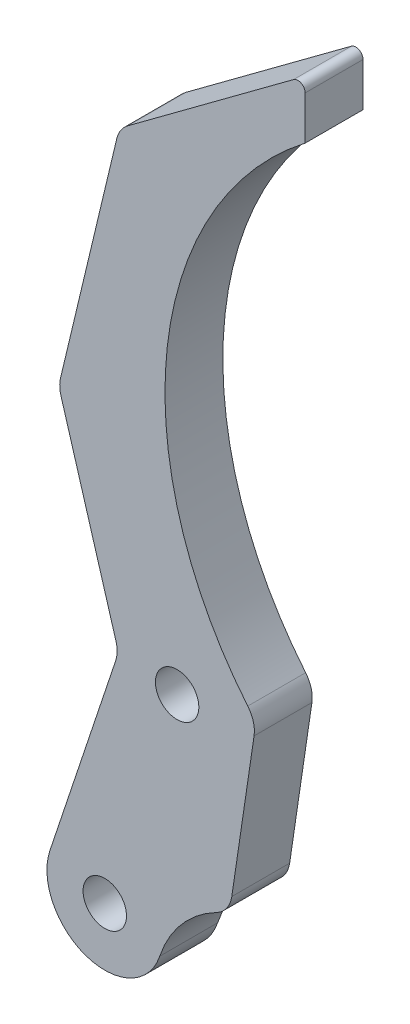
SolidWorks part; units mm, degrees
ref_plane "前视基准面" through (0, 0, 0) normal (0, 0, 1) x (1, 0, 0)
ref_plane "上视基准面" through (0, 0, 0) normal (0, 1, 0) x (1, 0, 0)
ref_plane "右视基准面" through (0, 0, 0) normal (1, 0, 0) x (0, 0, -1)
sketch "草图1" plane through (0, 0, 0) normal (0, 0, 1) x (1, 0, 0)
  line L1 (-44.759, 0) -> (37.6123, 0) construction
  line L2 (0, 0) -> (0, 68.6572) construction
  line L3 (15.4812, 24.7175) -> (6.2807, 1.4721) construction
  line L4 (22.9197, 21.7734) -> (13.7193, -1.4721) construction
  line L5 (22.9952, 24.5104) -> (15.4057, 21.9805) construction
  line L6 (8.8834, 38.4304) -> (10.4236, 28.044) construction
  line L8 (22.9952, 24.5104) -> (18.4512, 38.1424) construction
  line L9 (18.4316, 39.345) -> (22.233, 52.1252) construction
  line L10 (22.2613, 53.1601) -> (18.3728, 69.4382) construction
  line L11 (11.411, 39.3495) -> (2.2105, 16.1041) construction
  line L12 (16.9899, 37.1414) -> (7.7895, 13.8959) construction
  line L13 (17.619, 70.5799) -> (6.1506, 79.0862) construction
  line L14 (5.3527, 78.6846) -> (5.3527, 75.678) construction
  line L15 (-15.4812, 24.7175) -> (-6.2807, 1.4721) construction
  line L16 (-22.9197, 21.7734) -> (-13.7193, -1.4721) construction
  line L17 (-16.9899, 37.1414) -> (-7.7895, 13.8959) construction
  line L18 (-11.411, 39.3495) -> (-2.2105, 16.1041) construction
  line L19 (-8.8834, 38.4304) -> (-10.4236, 28.044)
  line L20 (-22.9952, 24.5104) -> (-18.4512, 38.1424)
  line L25 (-18.4316, 39.345) -> (-22.233, 52.1252)
  line L26 (-5, 15) -> (-10, 0) construction
  line L27 (5, 15) -> (10, 0) construction
  line L28 (14.2005, 38.2455) -> (19.2005, 23.2455) construction
  line L29 (-22.2613, 53.1601) -> (-18.3728, 69.4382)
  line L30 (-17.619, 70.5799) -> (-6.1506, 79.0862)
  line L31 (-5.3527, 78.6846) -> (-5.3527, 75.678)
  line L32 (-9.9581, 55.9149) -> (14.9371, 53.6276) construction
  circle A0 centre (-10, 0) radius 10 construction
  circle A4 centre (0, 55) radius 15 construction
  circle A5 centre (10, 0) radius 4 construction
  circle A6 centre (10, 0) radius 10 construction
  arc A14 (15.4057, 21.9805) -> (10.5848, 26.9564) centre (7.8163, 19.4507) ccw construction
  circle A16 centre (19.2005, 23.2455) radius 1.5 construction
  circle A17 centre (19.2005, 23.2455) radius 4 construction
  circle A18 centre (5, 15) radius 3 construction
  arc A19 (9.3195, 39.9972) -> (5.3527, 75.678) centre (-9.9581, 55.9149) ccw construction
  circle A20 centre (14.2005, 38.2455) radius 3 construction
  circle A21 centre (-10, 0) radius 4 construction
  circle A22 centre (-19.2005, 23.2455) radius 1.5
  arc A23 (-22.9952, 24.5104) -> (-15.4057, 21.9805) centre (-19.2005, 23.2455) ccw
  arc A24 (-15.4057, 21.9805) -> (-11.4848, 26.56) centre (-7.8163, 19.4507) cw
  circle A25 centre (-14.2005, 38.2455) radius 3 construction
  circle A26 centre (-5, 15) radius 3 construction
  circle A28 centre (-14.2005, 38.2455) radius 1.5
  circle A29 centre (-5, 15) radius 1.5 construction
  circle A30 centre (5, 15) radius 1.5 construction
  circle A31 centre (14.2005, 38.2455) radius 1.5 construction
  arc A33 (-11.4848, 26.56) -> (-10.4236, 28.044) centre (-12.4019, 28.3373) ccw
  arc A40 (6.1506, 79.0862) -> (5.3527, 78.6846) centre (5.8527, 78.6846) ccw construction
  arc A41 (11.4848, 26.56) -> (10.4236, 28.044) centre (12.4019, 28.3373) cw construction
  arc A42 (8.8834, 38.4304) -> (9.3195, 39.9972) centre (10.8617, 38.7237) cw construction
  arc A43 (-9.3195, 39.9972) -> (-5.3527, 75.678) centre (9.9581, 55.9149) cw
  arc A44 (18.4512, 38.1424) -> (18.4316, 39.345) centre (20.3486, 38.7748) cw construction
  arc A45 (22.233, 52.1252) -> (22.2613, 53.1601) centre (20.316, 52.6954) ccw construction
  arc A46 (18.3728, 69.4382) -> (17.619, 70.5799) centre (16.4275, 68.9735) ccw construction
  arc A47 (-6.1506, 79.0862) -> (-5.3527, 78.6846) centre (-5.8527, 78.6846) cw
  arc A48 (-8.8834, 38.4304) -> (-9.3195, 39.9972) centre (-10.8617, 38.7237) ccw
  arc A49 (-18.4512, 38.1424) -> (-18.4316, 39.345) centre (-20.3486, 38.7748) ccw
  arc A50 (-22.233, 52.1252) -> (-22.2613, 53.1601) centre (-20.316, 52.6954) cw
  arc A51 (-18.3728, 69.4382) -> (-17.619, 70.5799) centre (-16.4275, 68.9735) cw
  point P71 (31.2517, 19.1606)
  point P72 (-18.5078, 23.7319)
  point P73 (23.0842, 24.6753)
  point P93 (5.3527, 79.678)
  point P96 (8.7498, 39.3313)
  point P99 (18.2518, 38.7406)
  point P102 (22.3858, 52.6388)
  point P105 (18.2036, 70.1462)
  point P109 (-5.3527, 79.678)
  point P112 (-8.7498, 39.3313)
  point P115 (-18.2518, 38.7406)
  point P118 (-10.5848, 26.9564)
  point P122 (-22.3858, 52.6388)
  point P125 (-18.2036, 70.1462)
  dimension "D1" = 30
  dimension "D3" = 20
  dimension "D4" = 25
  dimension "D5" = 8
  dimension "D6" = 3
  dimension "D7" = 2
  dimension "D8" = 8
  dimension "D13" = 25
  dimension "D20" = 140
  dimension "D21" = 6
  dimension "D27" = 3
  dimension "D29" = 0.5
  dimension "D28" = 16
  dimension "D30" = 2
  dimension "D31" = 55
  dimension "D14" = 4
  dimension "D12" = 10.5
  dimension "D18" = 150
  dimension "D10" = 0.5
  dimension "D26" = 2
  dimension "D9" = 11
  dimension "D11" = 15
  dimension "D15" = 10
  dimension "D16" = 145
  dimension "D17" = 14.5
  dimension "D19" = 18
  dimension "D22" = 5
  dimension "D23" = 15
  dimension "D24" = 25
  dimension "D25" = 4
extrude "凸台-拉伸1" add sketch "草图1" along normal blind 4
